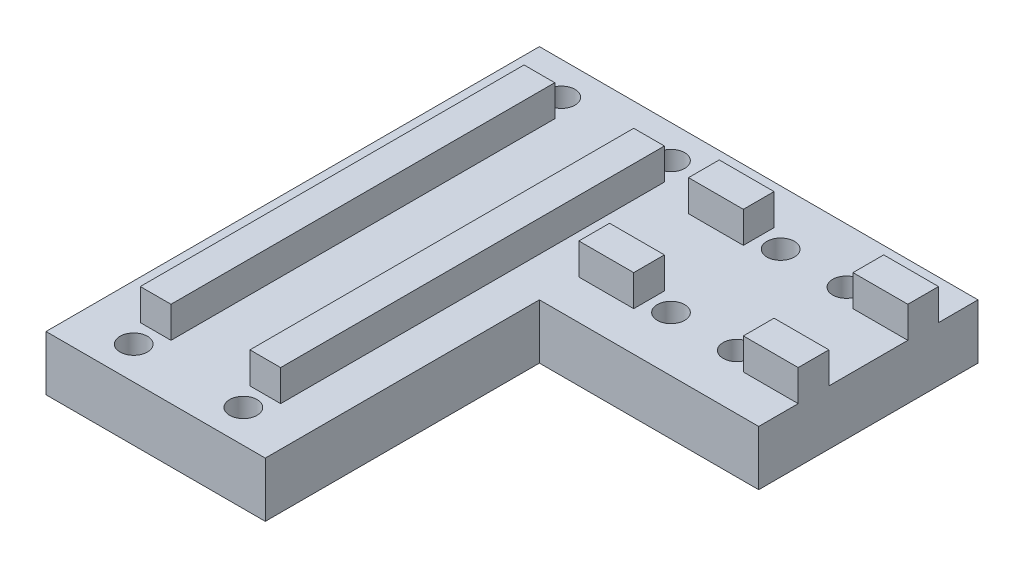
SolidWorks part; units mm, degrees
ref_plane "Alzado" through (0, 0, 0) normal (0, 0, 1) x (1, 0, 0)
ref_plane "Planta" through (0, 0, 0) normal (0, 1, 0) x (1, 0, 0)
ref_plane "Vista lateral" through (0, 0, 0) normal (1, 0, 0) x (0, 0, -1)
sketch "Croquis1" plane through (0, 0, 0) normal (0, 1, 0) x (1, 0, 0)
  line L1 (25, 20) -> (-65, 20)
  line L2 (25, 20) -> (25, -20)
  line L3 (-15, -20) -> (-65, -20)
  line L4 (-65, 20) -> (-65, -20)
  line L8 (25, -20) -> (25, -70)
  line L9 (25, -70) -> (-15, -70)
  line L10 (-15, -20) -> (-15, -70)
  point P0 (0, 0)
  dimension "D1" = 40
  dimension "D2" = 90
  dimension "D3" = 40
  dimension "D4" = 50
extrude "Saliente-Extruir1" add sketch "Croquis1" along normal blind 10
sketch "Croquis2" plane through (0, 0, 70) normal (0, 0, 1) x (1, 0, 0)
  line L27 (25, 10) -> (25, 0) construction
  line B0 (15, 15.7) -> (15, 1.4751) construction
  line B1 (12.2, 9.9874) -> (12.2, 15.7)
  line B2 (17.8, 15.7) -> (17.8, 9.9874)
  line B3 (15, 9.9874) -> (12.2, 9.9874)
  line B4 (12.2, 15.7) -> (17.8, 15.7)
  line B5 (17.8, 9.9874) -> (15, 9.9874)
  line B6 (-5, 15.7) -> (-5, 1.4751) construction
  line B7 (-7.8, 9.9874) -> (-7.8, 15.7)
  line B8 (-2.2, 15.7) -> (-2.2, 9.9874)
  line B9 (-5, 9.9874) -> (-7.8, 9.9874)
  line B10 (-7.8, 15.7) -> (-2.2, 15.7)
  line B11 (-2.2, 9.9874) -> (-5, 9.9874)
  dimension "D1" = 10
  dimension "D2" = 2
  dimension "D3" = 20
sketch_block_instance "Bloque1-1"
sketch_block "Bloque1" parameters "D1"=1.5, "D2"=4.6406
sketch_block_instance "Bloque1-2"
extrude "Saliente-Extruir2" add sketch "Croquis2" against normal through all
sketch "Croquis3" plane through (-65, 0, 0) normal (-1, 0, 0) x (0, 0, 1)
  line L13 (20, 10) -> (20, 0) construction
  line B0 (10, 15.7) -> (10, 10) construction
  line B1 (7.2, 10) -> (7.2, 15.7)
  line B2 (12.8, 15.7) -> (12.8, 10)
  line B3 (10, 10) -> (7.2, 10)
  line B4 (7.2, 15.7) -> (12.8, 15.7)
  line B5 (12.8, 10) -> (10, 10)
  line B6 (-12.8, 10) -> (-12.8, 15.7)
  line B7 (-7.2, 15.7) -> (-7.2, 10)
  line B8 (-10, 10) -> (-12.8, 10)
  line B9 (-12.8, 15.7) -> (-7.2, 15.7)
  line B10 (-7.2, 10) -> (-10, 10)
  dimension "D1" = 10
  dimension "D2" = 2
  dimension "D3" = 20
sketch_block_instance "Bloque2-1"
sketch_block "Bloque2" parameters "D1"=1.5, "D2"=6.3541
sketch_block_instance "Bloque2-2"
extrude "Saliente-Extruir3" add sketch "Croquis3" against normal blind 50
sketch "Croquis6" plane through (-65, 0, 0) normal (-1, 0, 0) x (0, 0, 1)
  line L1 (-28.4643, 27.9616) -> (28.4643, 27.9616)
  line L2 (-28.4643, 27.9616) -> (-28.4643, -27.9616)
  line L3 (-28.4643, -27.9616) -> (28.4643, -27.9616)
  line L4 (28.4643, 27.9616) -> (28.4643, -27.9616)
  line L5 (-28.4643, 27.9616) -> (28.4643, -27.9616) construction
  line L6 (-28.4643, -27.9616) -> (28.4643, 27.9616) construction
extrude "Cortar-Extruir2" cut sketch "Croquis6" against normal blind 30
sketch "Croquis5" plane through (0, 15.7, 0) normal (0, 1, 0) x (1, 0, 0)
  line L0 (-15, -20) -> (-15, -70) construction
  line L1 (-15, -70) -> (25, -70)
  line L2 (-15, -70) -> (-15, -60)
  line L3 (-15, -60) -> (25, -60)
  line L4 (25, -70) -> (25, -60)
  line L5 (25, -70) -> (25, 20) construction
  line L24 (25, -70) -> (25, 20) construction
  line L25 (25, 20) -> (-15, 20)
  line L26 (25, 20) -> (25, 10)
  line L27 (25, 10) -> (-15, 10)
  line L28 (-15, 20) -> (-15, 10)
  line L29 (12.2, 20) -> (-2.2, 20) construction
  line L31 (-2.2, -70) -> (12.2, -70) construction
  line L32 (-35, -7.2) -> (-35, 7.2) construction
  line L33 (-25, 20) -> (-35, 20)
  line L34 (-25, 20) -> (-25, -20)
  line L35 (-25, -20) -> (-35, -20)
  line L36 (-35, 20) -> (-35, -20)
  line L37 (-25, 20) -> (-35, -20) construction
  line L38 (-25, -20) -> (-35, 20) construction
  line L39 (-7.8, 20) -> (-35, 20) construction
  line L40 (-35, -20) -> (-15, -20) construction
  point P14 (-30, 0)
  dimension "D1" = 10
  dimension "10" = 10
  dimension "D3" = 10
extrude "Cortar-Extruir1" cut sketch "Croquis5" against normal up to surface (5.7 mm away) up to face at (-22.5429, 10, 10)
sketch "Croquis7" plane through (0, 10, 0) normal (0, 1, 0) x (1, 0, 0)
  line L0 (-35, -20) -> (-15, -20) construction
  line L1 (-15, -20) -> (-15, -70) construction
  line L2 (25, -70) -> (25, 20) construction
  line L3 (-35, -20) -> (-35, 20) construction
  line L4 (-15, -70) -> (25, -70) construction
  line L5 (25, 20) -> (-35, 20) construction
  circle A0 centre (-29, 10) radius 2.5
  circle A1 centre (-29, -10) radius 2.5
  circle A2 centre (15, 14) radius 2.5
  circle A3 centre (-5, 14) radius 2.5
  circle A4 centre (-5, -64) radius 2.5
  circle A5 centre (15, -64) radius 2.5
  dimension "D1" = 5
  dimension "D2" = 10
  dimension "D3" = 20
  dimension "D4" = 10
  dimension "D5" = 20
  dimension "D6" = 10
  dimension "D7" = 20
  dimension "D8" = 6
  dimension "D9" = 6
  dimension "D10" = 6
extrude "Cortar-Extruir3" cut sketch "Croquis7" against normal through all
mirror "Mirror1" about plane through (-35, 0, 0) normal (-1, 0, 0) of bodies 118
sketch "Sketch1" plane through (25, 0, 0) normal (1, 0, 0) x (0, 0, -1)
  line L1 (78.2609, -20.0969) -> (-78.2609, -20.0969)
  line L2 (78.2609, -20.0969) -> (78.2609, 20.0969)
  line L3 (78.2609, 20.0969) -> (-78.2609, 20.0969)
  line L4 (-78.2609, -20.0969) -> (-78.2609, 20.0969)
  line L5 (78.2609, -20.0969) -> (-78.2609, 20.0969) construction
  line L6 (78.2609, 20.0969) -> (-78.2609, -20.0969) construction
  point P0 (0, 0)
extrude "Cut-Extrude1" cut sketch "Sketch1" against normal up to surface (40 mm away) up to face at (-15, 5, 45)
